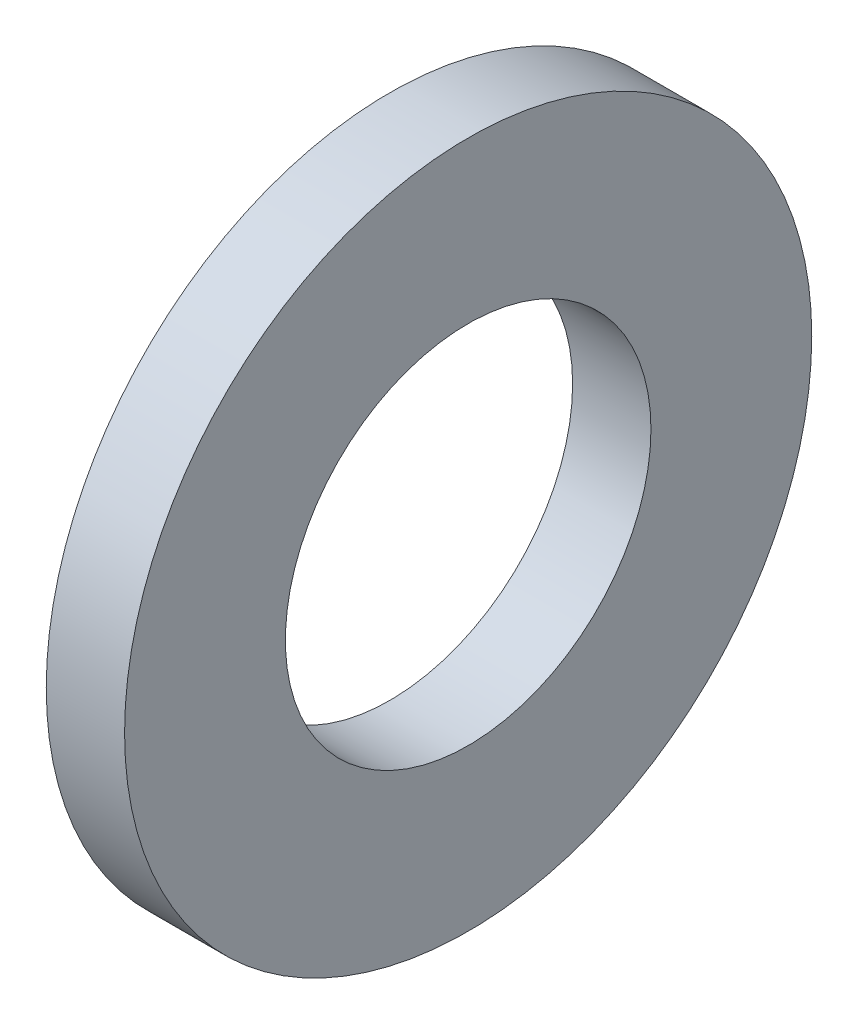
SolidWorks part; units mm, degrees
ref_plane "Front Plane" through (0, 0, 0) normal (0, 0, 1) x (1, 0, 0)
ref_plane "Top Plane" through (0, 0, 0) normal (0, 1, 0) x (1, 0, 0)
ref_plane "Right Plane" through (0, 0, 0) normal (1, 0, 0) x (0, 0, -1)
sketch "Sketch1" plane through (0, 0, 0) normal (1, 0, 0) x (0, 0, -1)
  circle A0 centre (0, 0) radius 6.35
  circle A1 centre (0, 0) radius 3.3782
  dimension "OD" = 12.7
  dimension "ID" = 6.7564
extrude "Boss-Extrude1" add sketch "Sketch1" along normal blind 1.4478
